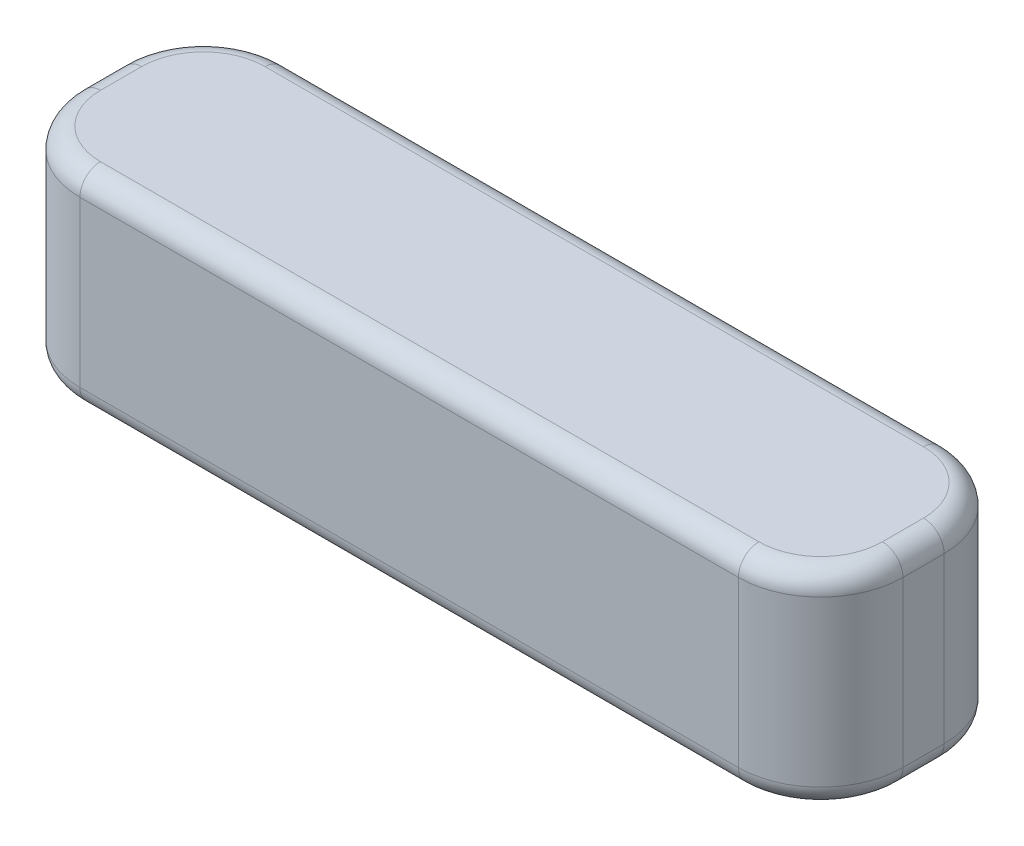
SolidWorks part; units mm, degrees
material "鑄碳鋼"
ref_plane "Front Plane" through (0, 0, 0) normal (0, 0, 1) x (1, 0, 0)
ref_plane "Top Plane" through (0, 0, 0) normal (0, 1, 0) x (1, 0, 0)
ref_plane "Right Plane" through (0, 0, 0) normal (1, 0, 0) x (0, 0, -1)
sketch "草圖1" plane through (0, 0, 0) normal (0, 1, 0) x (1, 0, 0)
  line L1 (-10, 2.5) -> (10, 2.5)
  line L2 (-10, 2.5) -> (-10, -2.5)
  line L3 (-10, -2.5) -> (10, -2.5)
  line L4 (10, 2.5) -> (10, -2.5)
  line L5 (-10, 2.5) -> (10, -2.5) construction
  line L6 (-10, -2.5) -> (10, 2.5) construction
  point P0 (0, 0)
  dimension "D1" = 20
  dimension "D2" = 5
extrude "填料-伸長1" add sketch "草圖1" along normal blind 5
fillet "圓角1" radius 2 4 edges at (-10, 2.5, -2.5) (-10, 2.5, 2.5) (10, 2.5, 2.5) (10, 2.5, -2.5)
fillet "圓角2" radius 0.5 16 edges at (-9.4142, 0, 1.9142) (-10, 0, 0) (-9.4142, 0, -1.9142) (0, 0, -2.5) (9.4142, 0, -1.9142) (10, 0, 0) (9.4142, 0, 1.9142) (-9.4142, 5, 1.9142) (-10, 5, 0) (-9.4142, 5, -1.9142) (0, 5, -2.5) (9.4142, 5, -1.9142) (10, 5, 0) (9.4142, 5, 1.9142) (0, 0, 2.5) (0, 5, 2.5)
